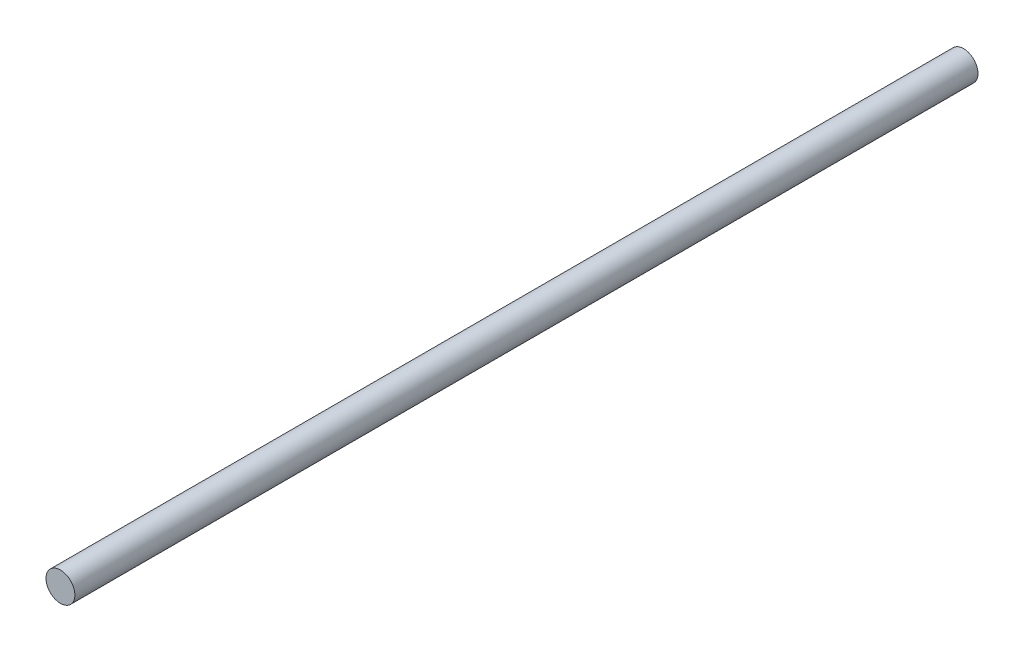
SolidWorks part; units mm, degrees
ref_plane "Ön Düzlem" through (0, 0, 0) normal (0, 0, 1) x (1, 0, 0)
ref_plane "Üst Düzlem" through (0, 0, 0) normal (0, 1, 0) x (1, 0, 0)
ref_plane "Sağ Düzlem" through (0, 0, 0) normal (1, 0, 0) x (0, 0, -1)
sketch "Çizim1" plane through (0, 0, 0) normal (0, 0, 1) x (1, 0, 0)
  circle A0 centre (0, 0) radius 4
  dimension "D1" = 8
extrude "Yükseklik-Ekstrüzyon1" add sketch "Çizim1" along normal blind 250
